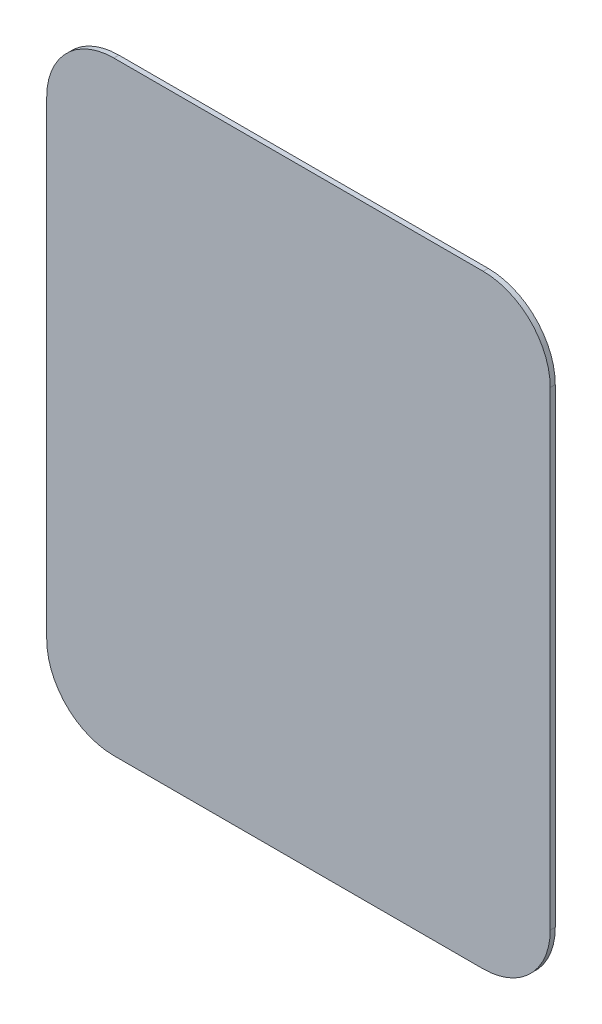
SolidWorks part; units mm, degrees
ref_plane "Alzado" through (0, 0, 0) normal (0, 0, 1) x (1, 0, 0)
ref_plane "Planta" through (0, 0, 0) normal (0, 1, 0) x (1, 0, 0)
ref_plane "Vista lateral" through (0, 0, 0) normal (1, 0, 0) x (0, 0, -1)
sketch "Croquis1" plane through (0, 0, 0) normal (0, 0, 1) x (1, 0, 0)
  line L1 (-47.7083, 74.7396) -> (62.2917, 74.7396)
  line L2 (-67.7083, 54.7396) -> (-67.7083, -85.2604)
  line L3 (-47.7083, -105.2604) -> (62.2917, -105.2604)
  line L4 (82.2917, 54.7396) -> (82.2917, -85.2604)
  arc A0 (-67.7083, 54.7396) -> (-47.7083, 74.7396) centre (-47.7083, 54.7396) cw
  arc A1 (82.2917, 54.7396) -> (62.2917, 74.7396) centre (62.2917, 54.7396) ccw
  arc A2 (62.2917, -105.2604) -> (82.2917, -85.2604) centre (62.2917, -85.2604) ccw
  arc A3 (-67.7083, -85.2604) -> (-47.7083, -105.2604) centre (-47.7083, -85.2604) ccw
  point P6 (-67.7083, 74.7396)
  point P9 (82.2917, 74.7396)
  point P12 (82.2917, -105.2604)
  dimension "D3" = 20
  dimension "D4" = 20
  dimension "D5" = 20
  dimension "D6" = 20
  dimension "D1" = 150
  dimension "D2" = 180
extrude "Saliente-Extruir1" add sketch "Croquis1" along normal blind 1.5 contours L1 A1 L4 A2 L3 A3 L2 A0
sketch "Croquis2" plane through (0, 0, 0) normal (0, 0, -1) x (-1, 0, 0)
  line L1 (47.7083, 74.7396) -> (-62.2917, 74.7396) construction
  line L2 (67.7083, 54.7396) -> (67.7083, -85.2604) construction
  line L3 (-82.2917, 54.7396) -> (-82.2917, -85.2604) construction
  line L4 (47.7083, -105.2604) -> (-62.2917, -105.2604) construction
  circle A0 centre (-47.7917, 45.2396) radius 2.5
  circle A1 centre (33.2083, 45.2396) radius 2.5
  circle A2 centre (33.2083, -75.7604) radius 2.5
  circle A3 centre (-47.7917, -75.7604) radius 2.5
  dimension "D1" = 5
  dimension "D2" = 5
  dimension "D3" = 5
  dimension "D4" = 5
  dimension "D5" = 29.5
  dimension "D6" = 34.5
  dimension "D7" = 34.5
  dimension "D8" = 34.5
  dimension "D9" = 34.5
  dimension "D10" = 29.5
  dimension "D11" = 29.5
  dimension "D12" = 29.5
extrude "Cortar-Extruir1" cut sketch "Croquis2" against normal blind 1.4
